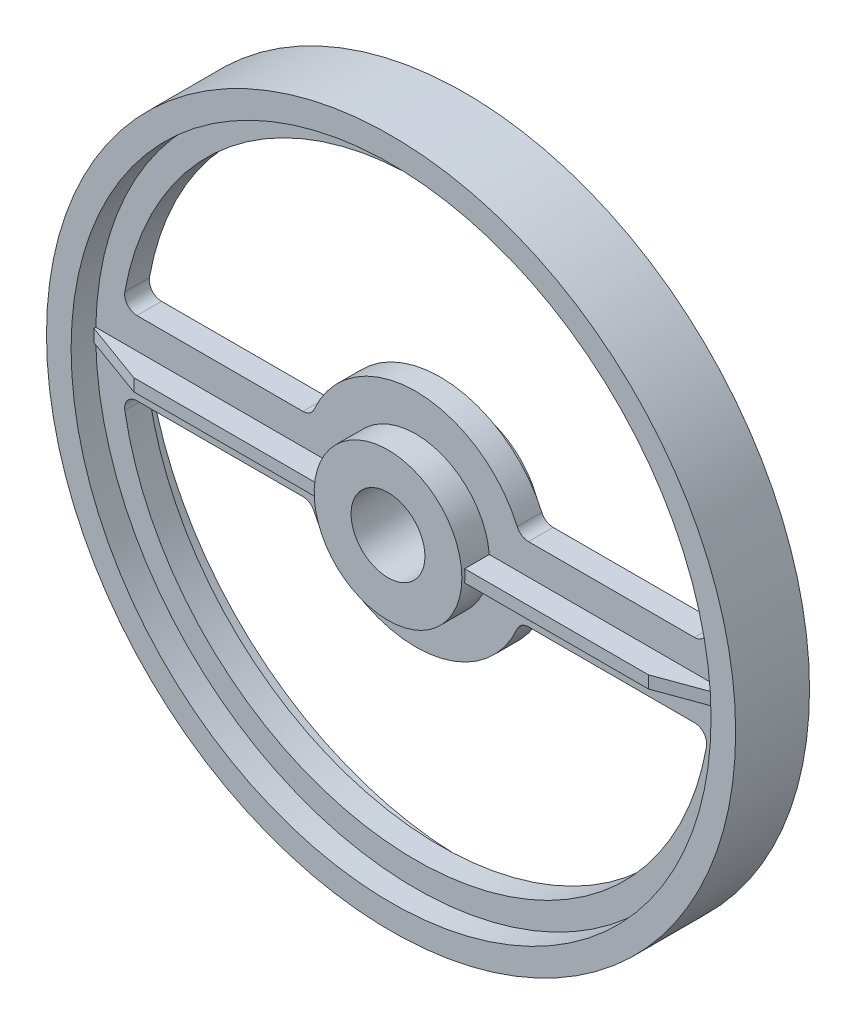
SolidWorks part; units mm, degrees
extrude "CenterHub" add sketch "Sketch1" along normal mid plane 41.275
sketch "Sketch1" plane through (0, 0, 0) normal (0, 0, 1) x (1, 0, 0)
  circle A0 centre (0, 0) radius 38.1
  dimension "D1" = 76.2
revolve "Rim and Web" add sketch "Sketch2" angle 360 about L0
sketch "Sketch2" plane through (0, 0, 0) normal (1, 0, 0) x (0, 0, -1)
  line L0 (0, 0) -> (51.266, 0) construction
  line L1 (-6.35, 0) -> (6.35, 0)
  line L2 (-6.35, 0) -> (-6.35, 165.1)
  line L3 (-6.35, 165.1) -> (-19.05, 165.1)
  line L4 (6.35, 165.1) -> (6.35, 0)
  line L5 (-19.05, 177.8) -> (19.05, 177.8)
  line L6 (-19.05, 177.8) -> (-19.05, 165.1)
  line L7 (19.05, 165.1) -> (6.35, 165.1)
  line L8 (19.05, 165.1) -> (19.05, 177.8)
  line L9 (0, 0) -> (0, 95.9354) construction
  dimension "D1" = 355.6
  dimension "D2" = 12.7
  dimension "D3" = 38.1
  dimension "D4" = 12.7
ref_plane "Plane1" through (0, 0, 0) normal (0, 0, 1) x (1, 0, 0)
ref_plane "Plane2" through (0, 0, 0) normal (0, 1, 0) x (1, 0, 0)
ref_plane "Plane3" through (0, 0, 0) normal (1, 0, 0) x (0, 0, -1)
other "Configuration Table"
sketch "Sketch3" plane through (0, 0, 0) normal (0, 1, 0) x (1, 0, 0)
  line L0 (0, 0) -> (193.8767, 0) construction
  line L1 (0, -19.05) -> (132.747, -19.05)
  line L2 (132.747, -19.05) -> (167.64, -6.35)
  line L3 (165.1, -6.35) -> (-165.1, -6.35) construction
  line L4 (167.64, -6.35) -> (167.64, 6.35)
  line L5 (132.747, 19.05) -> (167.64, 6.35)
  line L6 (0, 19.05) -> (132.747, 19.05)
  line L7 (0, -19.05) -> (0, 19.05)
  line L8 (165.1, -19.05) -> (-165.1, -19.05) construction
  line L9 (165.1, -19.05) -> (165.1, -6.35) construction
  point P10 (167.64, 0)
  dimension "D1" = 20
  dimension "D2" = 2.54
extrude "Rib" add sketch "Sketch3" along normal mid plane 6.35
sketch "Sketch4" plane through (0, 0, 0) normal (0, 0, 1) x (1, 0, 0)
  line L0 (0, 0) -> (202.3803, 0) construction
  line L1 (0, 0) -> (-192.8971, 0) construction
  line L2 (-151.2047, -19.05) -> (-53.8815, -19.05)
  line L3 (151.2047, -19.05) -> (53.8815, -19.05)
  circle A1 centre (0, 0) radius 57.15
  arc A3 (-53.8815, -19.05) -> (53.8815, -19.05) centre (0, 0) ccw
  circle A4 centre (0, 0) radius 152.4
  arc A5 (-151.2047, -19.05) -> (151.2047, -19.05) centre (0, 0) ccw
  dimension "D1" = 19.05
  dimension "D2" = 19.05
  dimension "D5" = 180
  dimension "D3" = 19.05
  dimension "D4" = 12.7
extrude "Lightening hole" cut sketch "Sketch4" against normal through all and the other way through all
fillet "Fillet1" radius 6.35 4 edges at (151.2047, -19.05, 0) (-151.2047, -19.05, 0) (-53.8815, -19.05, 0) (53.8815, -19.05, 0)
pattern_circular "CirPattern1" count 2 every 180 about axis through (0, 0, 0) along (0, 0, 1) of "Lightening hole", "Fillet1", "Rib"
sketch "Sketch5" plane through (0, 0, 0) normal (0, 0, 1) x (1, 0, 0)
  circle A0 centre (0, 0) radius 19.05
  dimension "D1" = 38.1
extrude "Thru hole" cut sketch "Sketch5" against normal through all and the other way through all
equation "\"D1@CirPattern1\" = 360 / \"D2@CirPattern1\""
equation "\"D5@Sketch4\" = \"D2@CirPattern1\""
